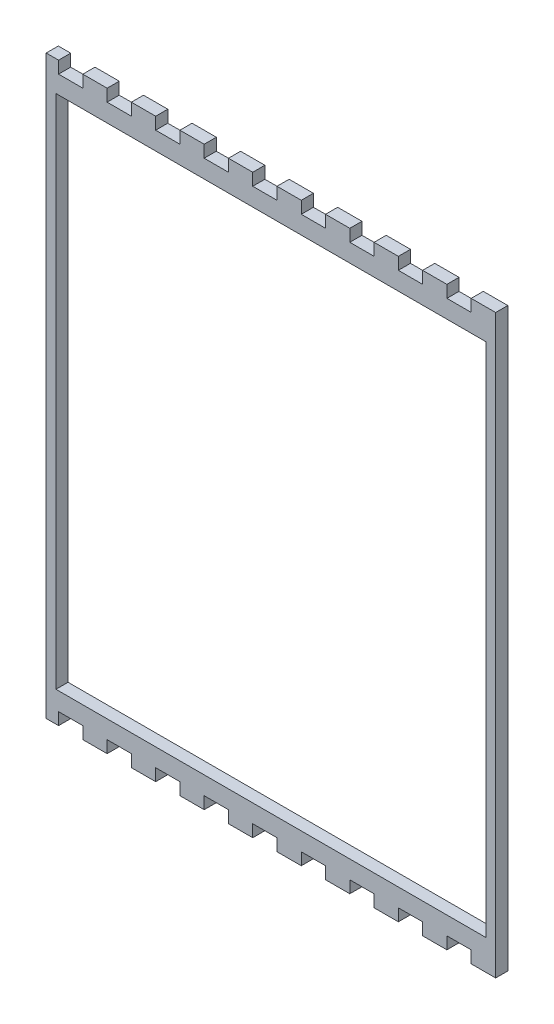
SolidWorks part; units mm, degrees
ref_plane "Front Plane" through (0, 0, 0) normal (0, 0, 1) x (1, 0, 0)
ref_plane "Top Plane" through (0, 0, 0) normal (0, 1, 0) x (1, 0, 0)
ref_plane "Right Plane" through (0, 0, 0) normal (1, 0, 0) x (0, 0, -1)
sketch "Model" plane through (0, 0, 0) normal (0, 0, 1) x (1, 0, 0)
  line L715 (1074.0804, 22.8602) -> (1079.9056, 22.8602)
  line L716 (1079.9056, 22.8602) -> (1079.9056, 28.5752)
  line L717 (1079.9056, 28.5752) -> (1091.3327, 28.5752)
  line L718 (1091.3327, 28.5752) -> (1091.3327, 22.8602)
  line L719 (1091.3327, 22.8602) -> (1102.7635, 22.8602)
  line L720 (1102.7635, 22.8602) -> (1102.7635, 28.5752)
  line L721 (1102.7635, 28.5752) -> (1114.1942, 28.5752)
  line L722 (1114.1942, 28.5752) -> (1114.1942, 22.8602)
  line L723 (1114.1942, 22.8602) -> (1125.6249, 22.8602)
  line L724 (1125.6249, 22.8602) -> (1125.6249, 28.5752)
  line L725 (1125.6249, 28.5752) -> (1137.0556, 28.5752)
  line L726 (1137.0556, 28.5752) -> (1137.0556, 22.8602)
  line L727 (1137.0556, 22.8602) -> (1148.4828, 22.8602)
  line L728 (1148.4828, 22.8602) -> (1148.4828, 28.5752)
  line L729 (1148.4828, 28.5752) -> (1159.9135, 28.5752)
  line L730 (1159.9135, 28.5752) -> (1159.9135, 22.8602)
  line L731 (1159.9135, 22.8602) -> (1171.3443, 22.8602)
  line L732 (1171.3443, 22.8602) -> (1171.3443, 28.5752)
  line L733 (1171.3443, 28.5752) -> (1182.775, 28.5752)
  line L734 (1182.775, 28.5752) -> (1182.775, 22.8602)
  line L735 (1182.775, 22.8602) -> (1194.2057, 22.8602)
  line L736 (1194.2057, 22.8602) -> (1194.2057, 28.5752)
  line L737 (1194.2057, 28.5752) -> (1205.6329, 28.5752)
  line L738 (1205.6329, 28.5752) -> (1205.6329, 22.8602)
  line L739 (1205.6329, 22.8602) -> (1217.0636, 22.8602)
  line L740 (1217.0636, 22.8602) -> (1217.0636, 28.5752)
  line L741 (1217.0636, 28.5752) -> (1228.4943, 28.5752)
  line L742 (1228.4943, 28.5752) -> (1228.4943, 22.8602)
  line L743 (1228.4943, 22.8602) -> (1239.925, 22.8602)
  line L744 (1239.925, 22.8602) -> (1239.925, 28.5752)
  line L745 (1239.925, 28.5752) -> (1251.3558, 28.5752)
  line L746 (1251.3558, 28.5752) -> (1251.3558, 22.8602)
  line L747 (1251.3558, 22.8602) -> (1262.7829, 22.8602)
  line L748 (1262.7829, 22.8602) -> (1262.7829, 28.5752)
  line L749 (1262.7829, 28.5752) -> (1274.2137, 28.5752)
  line L750 (1274.2137, 28.5752) -> (1274.2137, 22.8602)
  line L751 (1274.2137, 22.8602) -> (1280.0389, 22.8602)
  line L752 (1280.0389, 22.8602) -> (1285.7542, 22.8602)
  line L753 (1285.7542, 22.8602) -> (1285.7542, 28.5752)
  line L754 (1285.7542, 28.5752) -> (1285.7542, 288.5754)
  line L755 (1285.7542, 288.5754) -> (1285.7542, 294.2904)
  line L756 (1285.7542, 294.2904) -> (1280.0389, 294.2904)
  line L757 (1280.0389, 294.2904) -> (1274.2137, 294.2904)
  line L758 (1274.2137, 294.2904) -> (1274.2137, 288.5754)
  line L759 (1274.2137, 288.5754) -> (1262.7829, 288.5754)
  line L760 (1262.7829, 288.5754) -> (1262.7829, 294.2904)
  line L761 (1262.7829, 294.2904) -> (1251.3558, 294.2904)
  line L762 (1251.3558, 294.2904) -> (1251.3558, 288.5754)
  line L763 (1251.3558, 288.5754) -> (1239.925, 288.5754)
  line L764 (1239.925, 288.5754) -> (1239.925, 294.2904)
  line L765 (1239.925, 294.2904) -> (1228.4943, 294.2904)
  line L766 (1228.4943, 294.2904) -> (1228.4943, 288.5754)
  line L767 (1228.4943, 288.5754) -> (1217.0636, 288.5754)
  line L768 (1217.0636, 288.5754) -> (1217.0636, 294.2904)
  line L769 (1217.0636, 294.2904) -> (1205.6329, 294.2904)
  line L770 (1205.6329, 294.2904) -> (1205.6329, 288.5754)
  line L771 (1205.6329, 288.5754) -> (1194.2057, 288.5754)
  line L772 (1194.2057, 288.5754) -> (1194.2057, 294.2904)
  line L773 (1194.2057, 294.2904) -> (1182.775, 294.2904)
  line L774 (1182.775, 294.2904) -> (1182.775, 288.5754)
  line L775 (1182.775, 288.5754) -> (1171.3443, 288.5754)
  line L776 (1171.3443, 288.5754) -> (1171.3443, 294.2904)
  line L777 (1171.3443, 294.2904) -> (1159.9135, 294.2904)
  line L778 (1159.9135, 294.2904) -> (1159.9135, 288.5754)
  line L779 (1159.9135, 288.5754) -> (1148.4828, 288.5754)
  line L780 (1148.4828, 288.5754) -> (1148.4828, 294.2904)
  line L781 (1148.4828, 294.2904) -> (1137.0556, 294.2904)
  line L782 (1137.0556, 294.2904) -> (1137.0556, 288.5754)
  line L783 (1137.0556, 288.5754) -> (1125.6249, 288.5754)
  line L784 (1125.6249, 288.5754) -> (1125.6249, 294.2904)
  line L785 (1125.6249, 294.2904) -> (1114.1942, 294.2904)
  line L786 (1114.1942, 294.2904) -> (1114.1942, 288.5754)
  line L787 (1114.1942, 288.5754) -> (1102.7635, 288.5754)
  line L788 (1102.7635, 288.5754) -> (1102.7635, 294.2904)
  line L789 (1102.7635, 294.2904) -> (1091.3327, 294.2904)
  line L790 (1091.3327, 294.2904) -> (1091.3327, 288.5754)
  line L791 (1091.3327, 288.5754) -> (1079.9056, 288.5754)
  line L792 (1079.9056, 288.5754) -> (1079.9056, 294.2904)
  line L793 (1079.9056, 294.2904) -> (1074.0804, 294.2904)
  line L794 (1074.0804, 294.2904) -> (1074.0804, 288.5754)
  line L795 (1074.0804, 288.5754) -> (1074.0804, 28.5752)
  line L796 (1074.0804, 28.5752) -> (1074.0804, 22.8602)
extrude "Boss-Extrude1" add sketch "Model" along normal blind 5.715
sketch "Sketch2" plane through (0, 0, 0) normal (0, 0, -1) x (-1, 0, 0)
  line L8 (-1078.6673, 280.0753) -> (-1281.1673, 280.0753)
  line L9 (-1078.6673, 37.0753) -> (-1078.6673, 280.0753)
  line L10 (-1281.1673, 280.0753) -> (-1281.1673, 37.0753)
  line L11 (-1281.1673, 37.0753) -> (-1078.6673, 37.0753)
  line L12 (-1078.6673, 280.0753) -> (-1281.1673, 280.0753)
  line L13 (-1078.6673, 37.0753) -> (-1078.6673, 280.0753)
  line L14 (-1281.1673, 280.0753) -> (-1281.1673, 37.0753)
  line L15 (-1281.1673, 37.0753) -> (-1078.6673, 37.0753)
  dimension "D1" = 0.5
extrude "Cut-Extrude1" cut sketch "Sketch2" against normal through all
